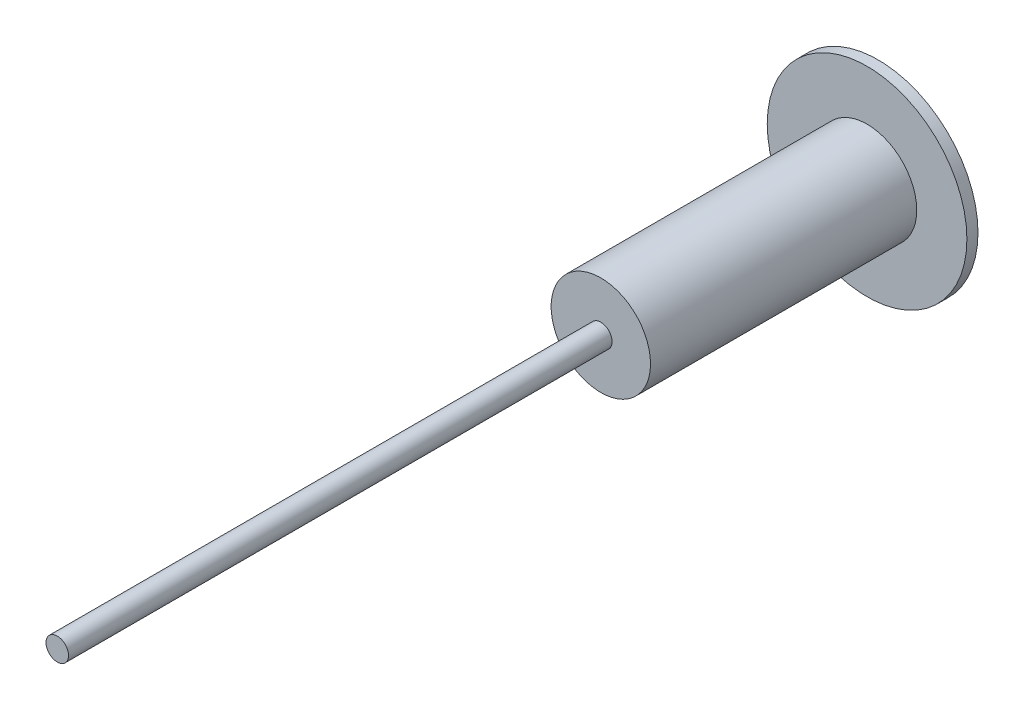
SolidWorks part; units mm, degrees
other "Markup1"
sketch "Sketch6" plane through (500, -500, -1363.6) normal (1, 0, 0) x (0, 0, -1)
ref_plane "Top Plane" through (0, 0, 0) normal (0, 0, 1) x (1, 0, 0)
ref_plane "Right Plane" through (0, 0, 0) normal (0, 1, 0) x (1, 0, 0)
ref_plane "Front Plane" through (0, 0, 0) normal (1, 0, 0) x (0, 0, -1)
sketch "Sketch1" plane through (0, 0, 0) normal (0, 0, 1) x (1, 0, 0)
  circle A0 centre (0, 0) radius 50.8
  dimension "D1" = 101.6
extrude "Boss-Extrude1" add sketch "Sketch1" against normal blind 2050 and the other way blind 1650
sketch "Sketch2" plane through (0, 0, -2050) normal (0, 0, 1) x (1, 0, 0)
  circle A0 centre (0, 0) radius 450
  dimension "D1" = 900
extrude "Boss-Extrude2" add sketch "Sketch2" along normal blind 50
sketch "Sketch3" plane through (0, 0, -2000) normal (0, 0, 1) x (1, 0, 0)
  circle A0 centre (0, 0) radius 223.901
  dimension "D1" = 447.802
extrude "Boss-Extrude3" add sketch "Sketch3" along normal blind 1200
